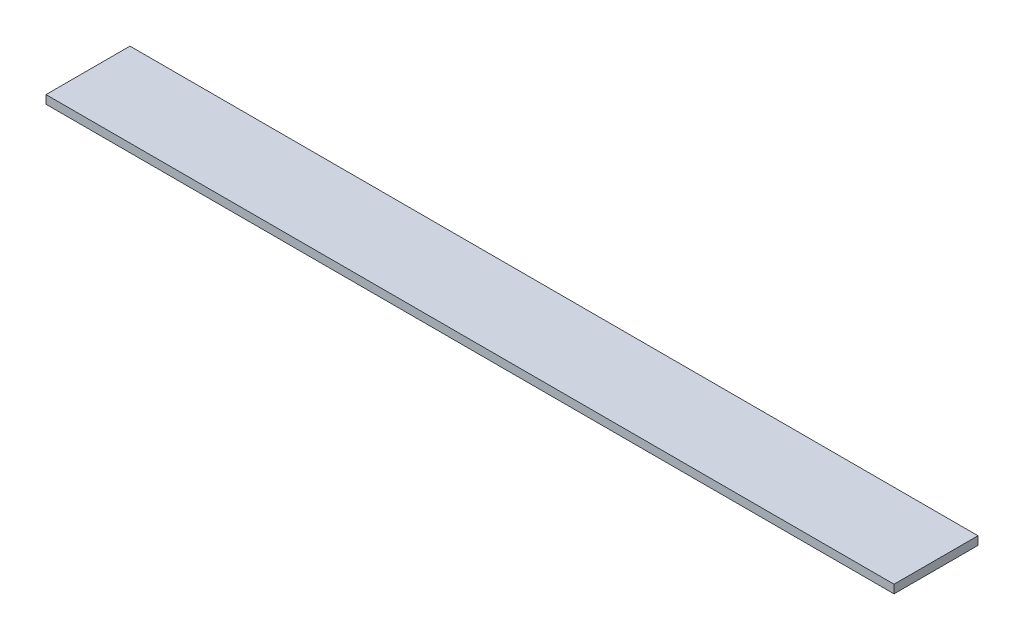
SolidWorks part; units mm, degrees
ref_plane "Front Plane" through (0, 0, 0) normal (0, 0, 1) x (1, 0, 0)
ref_plane "Top Plane" through (0, 0, 0) normal (0, 1, 0) x (1, 0, 0)
ref_plane "Right Plane" through (0, 0, 0) normal (1, 0, 0) x (0, 0, -1)
sketch "Sketch1" plane through (0, 0, 0) normal (0, 1, 0) x (1, 0, 0)
  line L0 (-505, 50) -> (505, -50) construction
  line L1 (-505, 50) -> (505, 50)
  line L2 (-505, 50) -> (-505, -50)
  line L3 (-505, -50) -> (505, -50)
  line L4 (505, 50) -> (505, -50)
  dimension "D1" = 1010
  dimension "D2" = 100
extrude "Boss-Extrude1" add sketch "Sketch1" along normal blind 10
